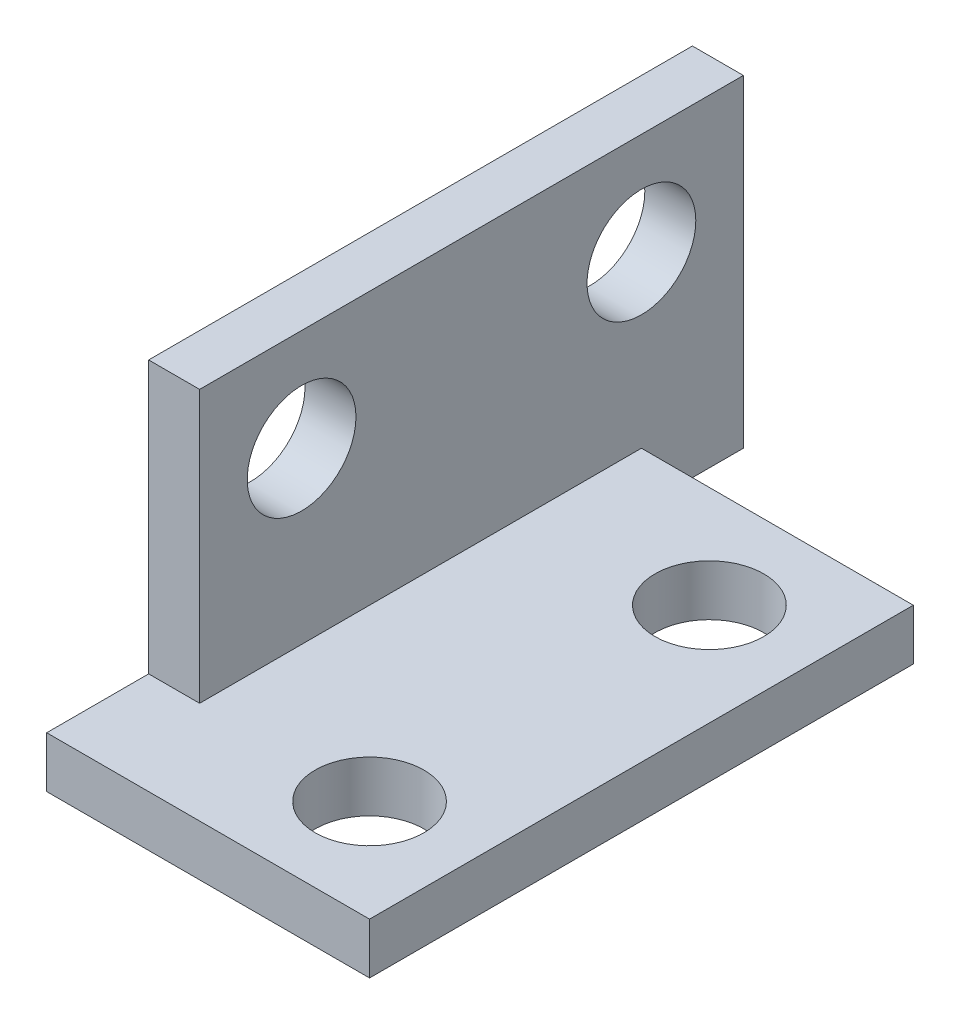
SolidWorks part; units mm, degrees
ref_plane "Front Plane" through (0, 0, 0) normal (0, 0, 1) x (1, 0, 0)
ref_plane "Top Plane" through (0, 0, 0) normal (0, 1, 0) x (1, 0, 0)
ref_plane "Right Plane" through (0, 0, 0) normal (1, 0, 0) x (0, 0, -1)
sketch "Sketch1" plane through (0, 0, 0) normal (0, 1, 0) x (1, 0, 0)
  line L4 (-3, 8) -> (-3, -13)
  line L5 (0, 8) -> (-3, 8)
  line L6 (-3, -13) -> (0, -13)
  line L8 (6.5, 0) -> (6.5, 8)
  line L9 (6.5, 8) -> (0, 8)
  line L10 (6.5, 0) -> (6.5, -13)
  line L11 (6.5, -13) -> (0, -13)
  circle A0 centre (0, 0) radius 1.6
  circle A1 centre (0, -10) radius 1.6
extrude "Boss-Extrude2" add sketch "Sketch1" along normal blind 1.5
sketch "Sketch3" plane through (0, 1.5, 0) normal (0, 1, 0) x (1, 0, 0)
  line L0 (6.5, 8) -> (5, 8)
  line L1 (6.5, 8) -> (-3, 8) construction
  line L2 (5, 8) -> (5, -13)
  line L3 (-3, -13) -> (6.5, -13) construction
  line L4 (5, -13) -> (6.5, -13)
  line L5 (6.5, -13) -> (6.5, 8)
extrude "Boss-Extrude3" add sketch "Sketch3" along normal blind 8
sketch "Sketch4" plane through (5, 0, 0) normal (-1, 0, 0) x (0, 0, 1)
  line L0 (-8, 9.5) -> (-8, 6.5)
  line L2 (-8, 9.5) -> (-8, 1.5) construction
  line L3 (-8, 6.5) -> (-5, 6.5)
  line L4 (-5, 6.5) -> (5, 6.5)
  circle A0 centre (-5, 6.5) radius 1.6
  circle A1 centre (5, 6.5) radius 1.6
extrude "Cut-Extrude2" cut sketch "Sketch4" against normal blind 8
sketch "Sketch6" plane through (5, 0, 0) normal (-1, 0, 0) x (0, 0, 1)
  line L0 (13, 9.5) -> (8, 9.5)
  line L1 (-8, 9.5) -> (13, 9.5) construction
  line L2 (8, 9.5) -> (8, 1.5)
  line L3 (-8, 1.5) -> (13, 1.5) construction
  line L4 (8, 1.5) -> (13, 1.5)
  line L5 (13, 1.5) -> (13, 9.5)
extrude "Cut-Extrude3" cut sketch "Sketch6" against normal blind 8
sketch "Sketch7" plane through (0, 1.5, 0) normal (0, 1, 0) x (1, 0, 0)
  line L0 (-3, 8) -> (-3, 3)
  line L1 (-3, 8) -> (-3, -13) construction
  line L2 (-3, 3) -> (5, 3)
  line L3 (5, 8) -> (5, -8) construction
  line L4 (5, 3) -> (5, 8)
  line L5 (5, 8) -> (-3, 8)
extrude "Cut-Extrude4" cut sketch "Sketch7" against normal blind 8
mirror "Mirror1" about plane through (6.5, 1.5, 0) normal (-1, 0, 0) of "Boss-Extrude3", "Cut-Extrude2", "Boss-Extrude2"
sketch "Sketch8" plane through (6.5, 0, 0) normal (-1, 0, 0) x (0, 0, 1)
  circle A0 centre (8, 1.5) radius 46.4801
extrude "Cut-Extrude5" cut sketch "Sketch8" along normal blind 64
sketch "Sketch9" plane through (8, 0, 0) normal (1, 0, 0) x (0, 0, -1)
  line L0 (-13, 9.5) -> (-8, 9.5)
  line L1 (8, 9.5) -> (-13, 9.5) construction
  line L2 (-8, 9.5) -> (-8, 1.5)
  line L3 (8, 1.5) -> (-13, 1.5) construction
  line L4 (-8, 1.5) -> (-13, 1.5)
  line L5 (-13, 1.5) -> (-13, 9.5)
extrude "Cut-Extrude6" cut sketch "Sketch9" against normal blind 64
sketch "Sketch10" plane through (0, 1.5, 0) normal (0, 1, 0) x (1, 0, 0)
  line L0 (16, 8) -> (16, 3)
  line L1 (16, 8) -> (16, -13) construction
  line L2 (16, 3) -> (8, 3)
  line L3 (8, 8) -> (8, -8) construction
  line L4 (8, 3) -> (8, 8)
  line L5 (8, 8) -> (16, 8)
extrude "Cut-Extrude7" cut sketch "Sketch10" against normal blind 64
sketch "Sketch11" plane through (8, 0, 0) normal (1, 0, 0) x (0, 0, -1)
  line L0 (5, 6.5) -> (3, 6.5)
  line L1 (-5, 6.5) -> (-7, 6.5)
  circle A0 centre (-7, 6.5) radius 1.6
  circle A1 centre (3, 6.5) radius 1.6
extrude "Cut-Extrude8" cut sketch "Sketch11" against normal blind 1.5
sketch "Sketch12" plane through (8, 0, 0) normal (1, 0, 0) x (0, 0, -1)
  line L0 (-8, 1.5) -> (-10, 1.5)
  line L1 (-10, 6.5) -> (-10, 9.5)
  line L2 (-10, 9.5) -> (-8, 9.5)
  line L3 (-8, 9.5) -> (-8, 7.749)
  line L4 (-10, 1.5) -> (-10, 6.5)
  line L6 (-8, 5.251) -> (-8, 1.5)
  circle A0 centre (-7, 6.5) radius 1.6
  arc A1 (-6, 5.251) -> (-6, 7.749) centre (-5, 6.5) ccw
  arc A2 (4, 5.251) -> (4, 7.749) centre (3, 6.5) ccw
  arc A3 (4, 5.251) -> (4, 7.749) centre (5, 6.5) ccw
  arc M2 (4, 5.251) -> (4, 7.749) centre (3, 6.5) cw
  arc M3 (4, 7.749) -> (4, 5.251) centre (5, 6.5) cw
  arc M4 (-6, 5.251) -> (-8, 5.251) centre (-7, 6.5) cw
  line M5 (-8, 5.251) -> (-8, 1.5)
  line M6 (-8, 1.5) -> (3, 1.5)
  line M7 (3, 1.5) -> (3, 0)
  line M8 (3, 0) -> (8, 0)
  line M9 (8, 0) -> (8, 9.5)
  line M10 (8, 9.5) -> (-8, 9.5)
  line M11 (-8, 9.5) -> (-8, 7.749)
  arc M12 (-8, 7.749) -> (-6, 7.749) centre (-7, 6.5) cw
  arc M13 (-6, 7.749) -> (-6, 5.251) centre (-5, 6.5) cw
extrude "Boss-Extrude5" add sketch "Sketch12" against normal up to surface (1.5 mm away) contours A0 L2 L1 L4 L0 M11 M5 | A0 M13 | A2 M3 | M13 M4 M5 M6 M7 M8 M9 M10 M11 M12 M3 M2
sketch "Sketch13" plane through (8, 0, 0) normal (1, 0, 0) x (0, 0, -1)
  line L0 (8, 9.5) -> (6, 9.5)
  line L1 (8, 9.5) -> (-10, 9.5) construction
  line L2 (6, 9.5) -> (6, 0)
  line L3 (3, 0) -> (8, 0) construction
  line L4 (6, 0) -> (8, 0)
  line L5 (8, 0) -> (8, 9.5)
extrude "Cut-Extrude9" cut sketch "Sketch13" against normal blind 1.5
sketch "Sketch15" plane through (0, 0, 0) normal (0, -1, 0) x (-1, 0, 0)
  line L0 (-13, 0) -> (-6.5, 0)
  line L1 (-6.5, -13) -> (-6.5, 6) construction
